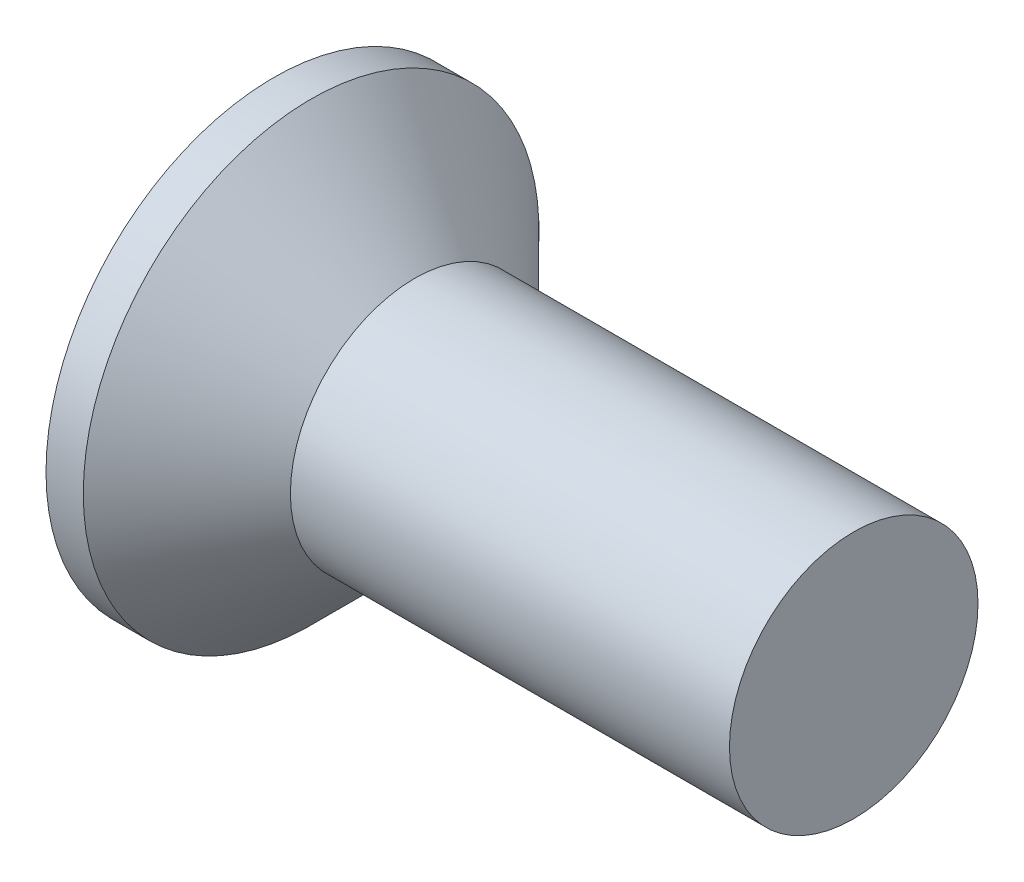
SolidWorks part; units mm, degrees
material "Alliage 7079"
ref_plane "Plane1" through (0, 0, 0) normal (0, 0, 1) x (1, 0, 0)
ref_plane "Plane2" through (0, 0, 0) normal (0, 1, 0) x (1, 0, 0)
ref_plane "Plane3" through (0, 0, 0) normal (1, 0, 0) x (0, 0, -1)
sketch "BodySke" plane through (0, 0, 0) normal (0, 0, 1) x (1, 0, 0)
  line L0 (0, 0) -> (0, 2.75)
  line L1 (0, 2.75) -> (0.45, 2.75)
  line L2 (1.7, 1.5) -> (7, 1.5)
  line L3 (7, 1.5) -> (7, 0)
  line L4 (7, 0) -> (0, 0)
  line L5 (-6.35, 0) -> (82.55, 0) construction
  line L6 (1.7, -1.5) -> (7, -1.5) construction
  line L7 (0.45, -2.75) -> (1.7, -1.5) construction
  line L8 (0.45, 2.75) -> (1.7, 1.5)
  line L9 (0, -2.75) -> (0.45, -2.75) construction
  line L10 (2.2, 3.0875) -> (2.2, -6.4375) construction
  line L11 (1, 6.35) -> (1, -3.175) construction
  dimension "Diameter" = 3
  dimension "Length" = 7
  dimension "Head_ht" = 1.7
  dimension "Head_dia" = 5.5
  dimension "Head_ang" = 90
  dimension "D6" = 0.45
  dimension "Advance" = 0.5
  dimension "Thread_nom" = 6
revolve "Base-Revolve" add sketch "BodySke" angle 360 about L5
cosmetic thread "ThreadCosmetic" [suppressed] parameters "Thread_length"=4.8, "Thread_minor"=2.439
sketch "Sketch2" plane through (0, 0, 0) normal (-1, 0, 0) x (0, 0, 1)
  line L0 (-2.75, -0.5) -> (2.75, -0.5)
  line L1 (-2.75, -0.5) -> (-2.75, 0.5)
  line L2 (2.75, 0.5) -> (-2.75, 0.5)
  line L3 (2.75, 0.5) -> (2.75, -0.5)
  dimension "D1" = 0.5
  dimension "Slot_width" = 1
  dimension "D2" = 5.5
  dimension "D3" = 2.75
extrude "Slot" [suppressed] cut sketch "Sketch2" against normal blind 0.9
sketch "Sketch3" plane through (0, 0, 0) normal (-1, 0, 0) x (0, 0, 1)
  line L0 (-0.395, 1.55) -> (0.395, 1.55)
  line L1 (0.395, 1.55) -> (0.395, -1.55)
  line L2 (0.395, -1.55) -> (-0.395, -1.55)
  line L3 (-0.395, -1.55) -> (-0.395, 1.55)
  dimension "D1" = 1.55
  dimension "Cross_dia" = 3.1
  dimension "D2" = 0.395
  dimension "Cross_width" = 0.79
ref_plane "Plane4" through (2.08, 0, 0) normal (-1, 0, 0) x (0, 0, 1)
sketch "Sketch4" plane through (2.08, 0, 0) normal (-1, 0, 0) x (0, 0, 1)
  line L0 (-0.1975, 0.1975) -> (0.1975, 0.1975)
  line L3 (0.1975, 0.1975) -> (0.1975, -0.1975)
  line L4 (0.1975, -0.1975) -> (-0.1975, -0.1975)
  line L5 (-0.1975, -0.1975) -> (-0.1975, 0.1975)
  dimension "D1" = 0.395
  dimension "D2" = 0.395
  dimension "D3" = 0.1975
  dimension "D4" = 0.1975
loft "Cross" cut profiles "Sketch3", "Sketch4"
pattern_circular "CirPattern1" count 2 every 90 about axis through (0, 0, 0) along (1, 0, 0) of "Cross"
sketch "ThdSchSke" plane through (0, 0, 0) normal (0, 0, 1) x (1, 0, 0)
  line L0 (2.2, -1.2195) -> (2.0036, -1.5)
  line L1 (2.2, -1.2195) -> (2.3964, -1.5)
  line L2 (2.3964, -1.5) -> (2.3964, -1.875)
  line L3 (-3.175, 0) -> (5.1513, 0) construction
  line L5 (2.3964, -1.875) -> (2.0036, -1.875)
  line L6 (2.0036, -1.875) -> (2.0036, -1.5)
  line L7 (0, 2.75) -> (0, -2.75) construction
  dimension "Thread_minor" = 2.439
  dimension "Diameter" = 3
  dimension "Start" = 2.2
  dimension "SideAngle" = 55
  dimension "VeeAngle" = 70
  dimension "Overcut" = 3.75
revolve "ThreadSchematic" [suppressed] cut sketch "ThdSchSke" angle 360 about L3
pattern_linear "ThdSchPat" [suppressed]
equation "\"D1@Sketch3\" = \"Cross_dia@Sketch3\" / 2"
equation "\"D2@Sketch3\" = \"Cross_width@Sketch3\" / 2"
equation "\"D1@Sketch4\" = \"Cross_width@Sketch3\" *.5"
equation "\"D2@Sketch4\" = \"D1@Sketch4\""
equation "\"D4@Sketch4\" = \"D2@Sketch4\" / 2"
equation "\"D3@Sketch4\" = \"D1@Sketch4\" / 2"
equation "\"D1@Sketch2\" = \"Slot_width@Sketch2\" / 2"
equation "\"D2@Sketch2\" = \"Head_dia@BodySke\""
equation "\"D3@Sketch2\" = \"D2@Sketch2\" / 2"
equation "\"Thread_length@ThreadCosmetic\" = ((sgn( (\"Length@BodySke\" - \"Advance@BodySke\" - \"Head_ht@BodySke\" ) - \"Thread_nom@BodySke\" )-1)*( (\"Length@BodySke\" - \"Advance@BodySke\" - \"Head_ht@BodySke\" ) - \"Thread_nom@BodySke\" ))/-2+ \"Thread_nom@BodySke\""
equation "\"Thread_minor@ThdSchSke\" = \"Thread_minor@ThreadCosmetic\""
equation "\"Diameter@ThdSchSke\" = \"Diameter@BodySke\""
equation "\"Overcut@ThdSchSke\" = \"Diameter@BodySke\" * 1.25"
equation "\"Start@ThdSchSke\" = 0.000001 + \"Length@BodySke\" - \"Thread_length@ThreadCosmetic\"  '---Countersunk---"
equation "\"Num_threads@ThdSchPat\" = int( \"Thread_length@ThreadCosmetic\" / \"Advance@BodySke\" + 0.999 )  + 1"
equation "\"Advance@ThdSchPat\" = \"Thread_length@ThreadCosmetic\" /  (\"Num_threads@ThdSchPat\" - 1) 'relax it"
